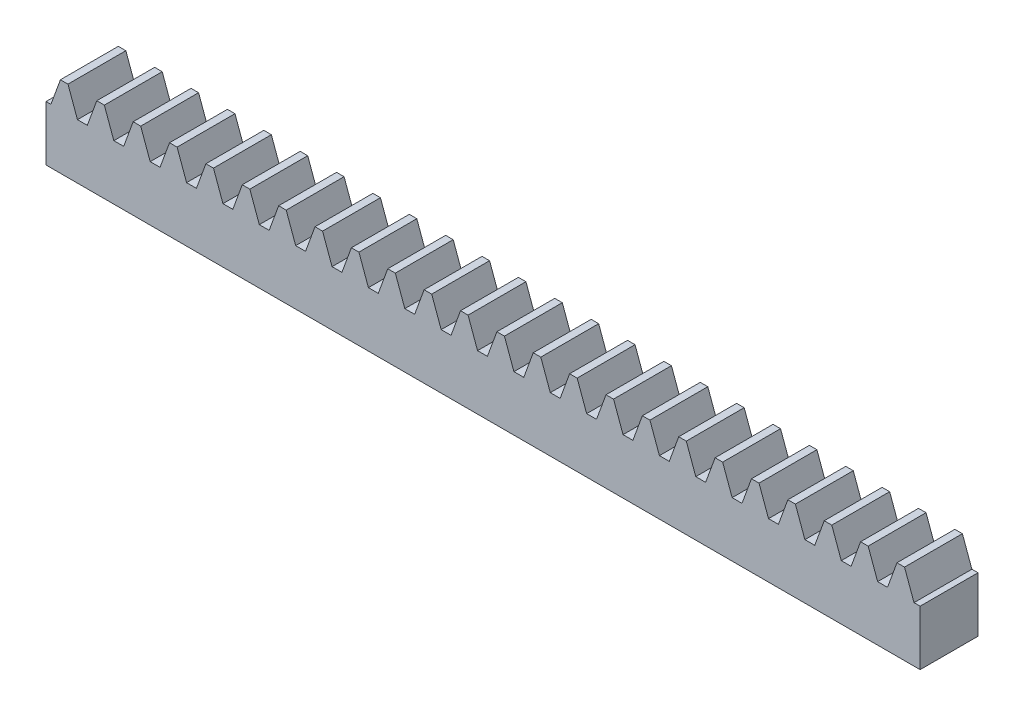
SolidWorks part; units mm, degrees
extrude "Blank" add sketch "BlankSke" against normal blind 20
sketch "BlankSke" plane through (0, 0, 0) normal (0, 0, 1) x (1, 0, 0)
  line L1 (0, 0) -> (302, 0)
  line L2 (0, 0) -> (0, 28)
  line L3 (0, 28) -> (302, 28)
  line L4 (302, 0) -> (302, 28)
  dimension "Length" = 302
  dimension "Blank_height" = 28
ref_plane "Plane1" through (0, 0, 0) normal (0, 0, 1) x (1, 0, 0)
ref_plane "Plane2" through (0, 0, 0) normal (0, 1, 0) x (1, 0, 0)
ref_plane "Plane3" through (0, 0, 0) normal (1, 0, 0) x (0, 0, -1)
sketch "HoldingSke" plane through (0, 0, 0) normal (0, 1, 0) x (1, 0, 0)
  line L0 (0, 0) -> (0.0348, 0.2476)
  line L1 (-15, 0) -> (100, 0) construction
  line L2 (0, 0) -> (-2.1039, 2.3779)
  line L3 (0, 0) -> (-11.863, 4.5341)
  line L4 (0, 0) -> (7.762, 3.7858)
  line L5 (0, 0) -> (-23.7986, -8.8762)
  line L6 (0, 0) -> (-10.5278, -7.1032)
  line L9 (-71.009, 38.7566) -> (212.7782, 142.0467)
  line L10 (-76.2, 6.3779) -> (-52.2, 6.3779)
  line L11 (0, 0) -> (-20, 0)
  line L12 (-76.2, 101.6) -> (-76.073, 101.6)
  line L13 (24.9733, 27.94) -> (52.9518, 28.4284)
  line L14 (24.9733, 27.94) -> (24.9743, 27.94)
  line L15 (24.9733, 27.94) -> (100.4006, 29.5858)
  circle A0 centre (0, 0) radius 19.05
  circle A1 centre (0, 0) radius 12
  circle A2 centre (0, 0) radius 12.7
  dimension "MPH" = 24
  dimension "Diameter" = 38.1
  dimension "Num_teeth" = 26
  dimension "Pitch" = 0.25
  dimension "Show_teeth" = 998
  dimension "Thickness" = 12.7
  dimension "Ap" = 20
  dimension "Pitch_height" = 24
  dimension "Width" = 20
  dimension "Backlash" = 0.127
  dimension "Addendum_fac" = 1
  dimension "Dedendum_fac" = 1.25
  dimension "Clearance_fac" = 0.25
  dimension "Dedendum_add" = 0.001
  dimension "Length" = 302
  dimension "Module" = 4
sketch "TooCutSkeIll" plane through (0, 0, 0) normal (0, 0, 1) x (1, 0, 0)
  line L0 (-4.9402, 27.8947) -> (-1.9425, 19.6586)
  line L1 (-1.0018, 19) -> (1.0018, 19)
  line L2 (1.9425, 19.6586) -> (4.9402, 27.8947)
  line L3 (302, 28) -> (0, 28) construction
  line L4 (0, 0) -> (0, 64.897) construction
  line L5 (-13.208, 24) -> (12.954, 24) construction
  line L6 (0, 0) -> (302, 0) construction
  line L7 (3.5226, 24) -> (3.5226, 48.7463) construction
  line L8 (-3.5226, 24) -> (-3.5226, 48.7463) construction
  line L9 (5.0905, 28) -> (5.0905, 28.0254)
  line L10 (-5.0905, 28) -> (-5.0905, 28.0254)
  line L11 (-5.0905, 28.0254) -> (5.0905, 28.0254)
  arc A0 (1.0018, 19) -> (1.9425, 19.6586) centre (1.0018, 20.001) ccw
  arc A1 (-1.9425, 19.6586) -> (-1.0018, 19) centre (-1.0018, 20.001) ccw
  arc A2 (5.0905, 28) -> (4.9402, 27.8947) centre (5.0905, 27.84) ccw
  arc A3 (-4.9402, 27.8947) -> (-5.0905, 28) centre (-5.0905, 27.84) ccw
  dimension "Pitch_height" = 24
  dimension "Addendum_plus" = 4.0254
  dimension "Pressure_angle" = 20
  dimension "Gap_width" = 7.0452
  dimension "Dedendum" = 5
extrude "ToothCutIll" [suppressed] cut sketch "TooCutSkeIll" against normal through all
sketch "TooCutSkeSim" plane through (0, 0, 0) normal (0, 0, 1) x (1, 0, 0)
  line L0 (1.7027, 19) -> (-1.7027, 19)
  line L1 (4.9877, 28.0254) -> (1.7027, 19)
  line L2 (0, 17.4625) -> (0, 53.467) construction
  line L3 (4.9877, 28.0254) -> (-4.9877, 28.0254)
  line L6 (-4.9877, 28.0254) -> (-1.7027, 19)
  line L9 (-3.5226, 24) -> (3.5226, 24) construction
  line L10 (0, 0) -> (302, 0) construction
  line L11 (3.5226, 24) -> (3.5226, 53.467) construction
  line L12 (-3.5226, 24) -> (-3.5226, 53.467) construction
  dimension "Pitch_height" = 24
  dimension "Addendum_plus" = 4.0254
  dimension "Pressure_angle" = 20
  dimension "Gap_width" = 7.0452
  dimension "Dedendum" = 5
extrude "ToothCutSim" cut sketch "TooCutSkeSim" against normal through all
pattern_linear "TeethCuts" count 25 spacing 12.5664 along (1, 0, 0) of "ToothCutIll", "ToothCutSim"
equation "' \"Module@HoldingSke\" = 6.35"
equation "' \"Num_teeth@HoldingSke\" = 12"
equation "' \"Ap@HoldingSke\" =  20"
equation "' \"Ap@HoldingSke\" = 20"
equation "' \"Width@HoldingSke\" = 0.25 * 25.4"
equation "' \"Show_teeth@HoldingSke\" = 500"
equation "' \"Backlash@HoldingSke\" = 0.009 * 25.4"
equation "' \"Addendum_fac@HoldingSke\" = 1.0"
equation "' \"Dedendum_fac@HoldingSke\" = 1.25"
equation "' \"Dedendum_add@HoldingSke\" = 0.00005 * 25.4"
equation "' \"Clearance_fac@HoldingSke\" = 0.25"
equation "' \"Pitch_height@HoldingSke\" = 1 * 25.4"
equation "' \"Length@HoldingSke\" = 4.71 * 25.4"
equation "\"Pitch@HoldingSke\" = 1 / \"Module@HoldingSke\""
equation "\"MPH@HoldingSke\" = \"Dedendum_fac@HoldingSke\" / \"Pitch@HoldingSke\" + 2 * \"Dedendum_add@HoldingSke\" + 0.002 * 25.4"
equation "\"MPH@HoldingSke\" = ((sgn( \"MPH@HoldingSke\" - \"Pitch_height@HoldingSke\")+1)*( \"MPH@HoldingSke\" - \"Pitch_height@HoldingSke\"))/2 + \"Pitch_height@HoldingSke\""
equation "\"Blank_height@BlankSke\" = \"Pitch_height@HoldingSke\" + \"Addendum_fac@HoldingSke\"  / \"Pitch@HoldingSke\" "
equation "\"Length@BlankSke\" =  \"Length@HoldingSke\""
equation "\"Face_width@Blank\" = \"Width@HoldingSke\""
equation "\"Pressure_angle@TooCutSkeIll\" = \"Ap@HoldingSke\""
equation "\"Addendum_plus@TooCutSkeIll\" =  \"Addendum_fac@HoldingSke\"  / \"Pitch@HoldingSke\" + 0.001 *25.4"
equation "\"Dedendum@TooCutSkeIll\" = \"Dedendum_fac@HoldingSke\"  / \"Pitch@HoldingSke\""
equation "\"Pitch_height@TooCutSkeIll\" =  \"MPH@HoldingSke\""
equation "\"Gap_width@TooCutSkeIll\" = 3.14159265 / 2 / \"Pitch@HoldingSke\" + 6 * \"Backlash@HoldingSke\""
equation "\"Pressure_angle@TooCutSkeSim\" = \"Ap@HoldingSke\""
equation "\"Addendum_plus@TooCutSkeSim\" =  \"Addendum_fac@HoldingSke\"  / \"Pitch@HoldingSke\" + 0.001 * 25.4"
equation "\"Dedendum@TooCutSkeSim\" = \"Dedendum_fac@HoldingSke\"  / \"Pitch@HoldingSke\""
equation "\"Pitch_height@TooCutSkeSim\" =  \"MPH@HoldingSke\""
equation "\"Gap_width@TooCutSkeSim\" = 3.14159265 / 2 / \"Pitch@HoldingSke\" + 6 * \"Backlash@HoldingSke\""
equation "\"Root_fillet@TooCutSkeIll\" = \"Clearance_fac@HoldingSke\" / \"Pitch@HoldingSke\" + \"Dedendum_add@HoldingSke\""
equation "\"Break_rad@TooCutSkeIll\" = 0.02 / \"Pitch@HoldingSke\" * 2"
equation "\"Linear_pitch@TeethCuts\" = 3.14159265 / \"Pitch@HoldingSke\""
equation "\"Num_teeth@HoldingSke\" = int( ( \"Length@HoldingSke\" + 0 ) / (3.14159265 / \"Pitch@HoldingSke\")) + 0.9999  + 1"
equation " \"Num_teeth@TeethCuts\" = int( \"Show_teeth@HoldingSke\" ) + 1"
equation " \"Num_teeth@TeethCuts\" = ((sgn( \"Num_teeth@TeethCuts\" - \"Num_teeth@HoldingSke\" )-1)*( \"Num_teeth@TeethCuts\" - \"Num_teeth@HoldingSke\" ))/-2+ \"Num_teeth@HoldingSke\""
equation " \"Num_teeth@TeethCuts\" = ((sgn( \"Num_teeth@TeethCuts\" - 2.0)+1)*( \"Num_teeth@TeethCuts\" - 2.0))/2 +2.0"
